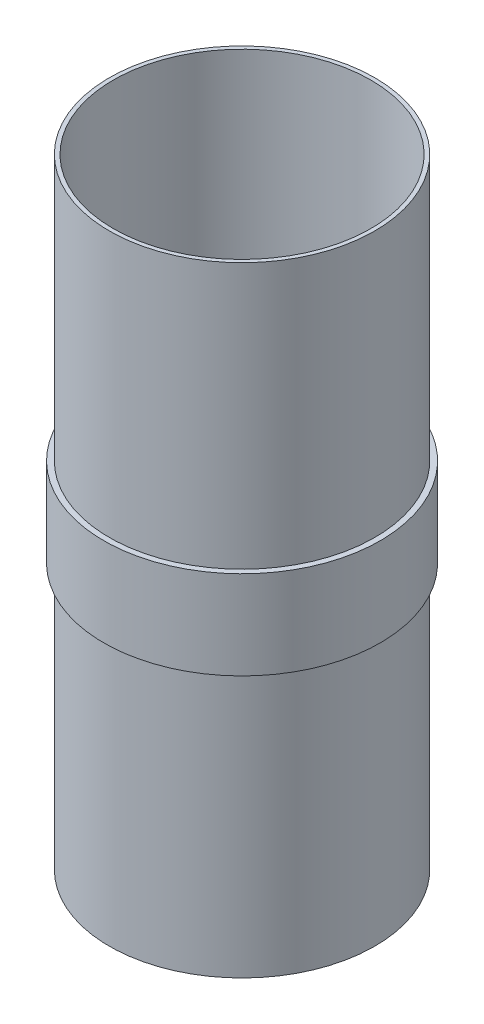
SolidWorks part; units mm, degrees
material "S-Glass Fiber"
ref_plane "Front Plane" through (0, 0, 0) normal (0, 0, 1) x (1, 0, 0)
ref_plane "Top Plane" through (0, 0, 0) normal (0, 1, 0) x (1, 0, 0)
ref_plane "Right Plane" through (0, 0, 0) normal (1, 0, 0) x (0, 0, -1)
other "Center of Mass"
sketch "Sketch1" plane through (0, 0, 0) normal (0, 0, 1) x (1, 0, 0)
  line L0 (0, 0) -> (73.914, 0) construction
  line L1 (73.914, 0) -> (73.914, 355.6)
  line L2 (73.914, 0) -> (76.2, 0)
  line L3 (76.2, 0) -> (76.2, 152.4)
  line L4 (76.2, 152.4) -> (79.375, 152.4)
  line L5 (79.375, 152.4) -> (79.375, 203.2)
  line L6 (79.375, 203.2) -> (76.2, 203.2)
  line L7 (76.2, 203.2) -> (76.2, 355.6)
  line L8 (76.2, 355.6) -> (73.914, 355.6)
  line L9 (0, 0) -> (0, 87.5598) construction
  dimension "D1" = 355.6
  dimension "D2" = 50.8
  dimension "D3" = 76.2
  dimension "D4" = 2.286
  dimension "D5" = 79.375
  dimension "D6" = 152.4
revolve "Revolve1" add sketch "Sketch1" angle 360 about L9
